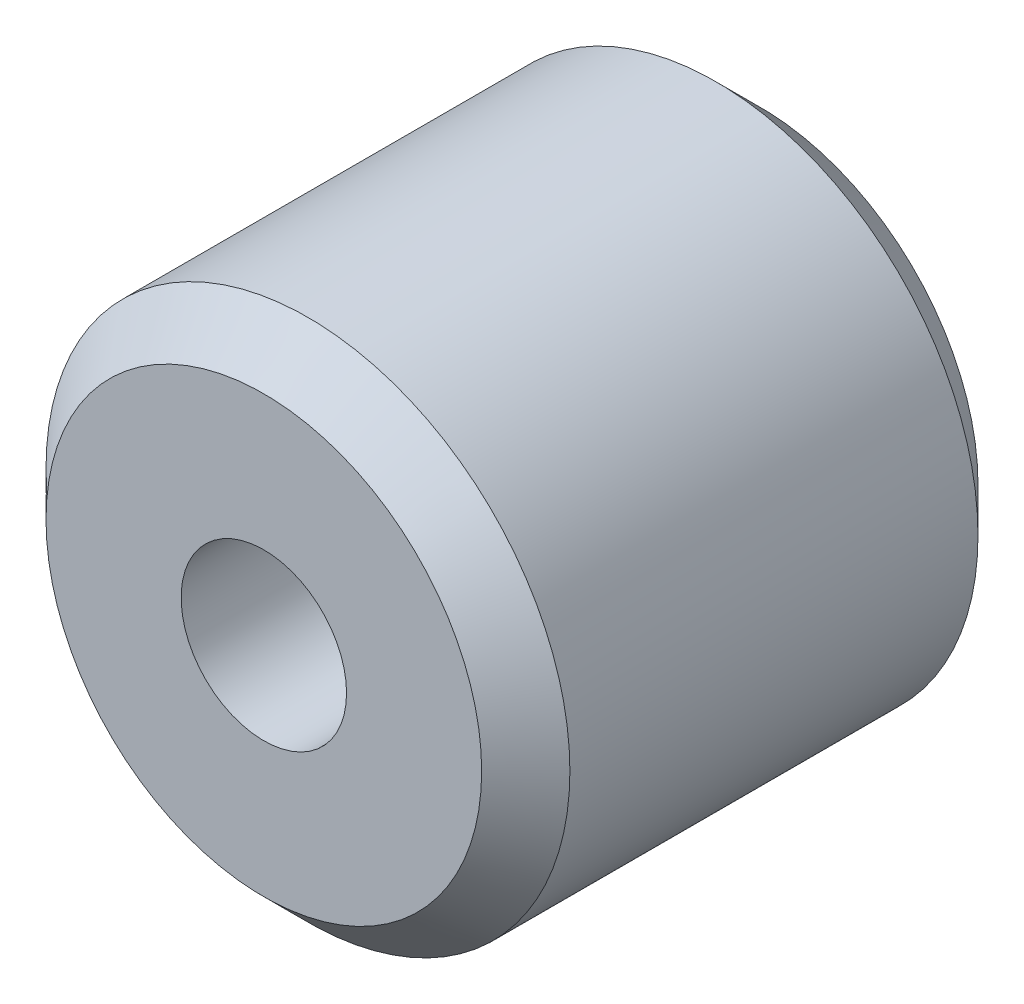
SolidWorks part; units mm, degrees
ref_plane "Front Plane" through (0, 0, 0) normal (0, 0, 1) x (1, 0, 0)
ref_plane "Top Plane" through (0, 0, 0) normal (0, 1, 0) x (1, 0, 0)
ref_plane "Right Plane" through (0, 0, 0) normal (1, 0, 0) x (0, 0, -1)
sketch "Sketch1" plane through (0, 0, 0) normal (0, 0, 1) x (1, 0, 0)
  circle A0 centre (0, 0) radius 4.75
  circle A1 centre (0, 0) radius 1.5
  dimension "D1" = 9.5
  dimension "D2" = 3
extrude "Boss-Extrude1" add sketch "Sketch1" along normal blind 9
chamfer "Chamfer1" distance 0.8 angle 45 2 edges at (4.75, 0, 0) (4.75, 0, 9)
